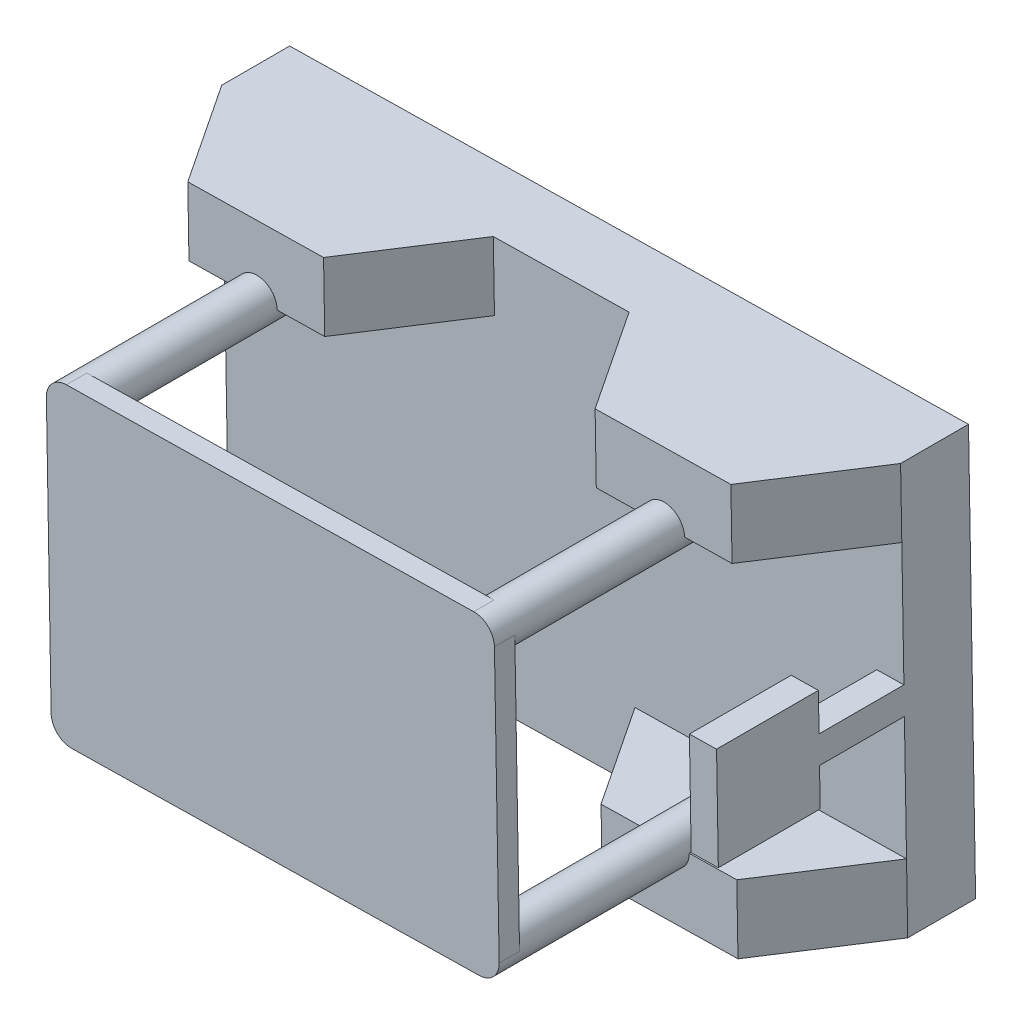
SolidWorks part; units mm, degrees
ref_plane "Front Plane" through (0, 0, 0) normal (0, 0, 1) x (1, 0, 0)
ref_plane "Top Plane" through (0, 0, 0) normal (0, 1, 0) x (1, 0, 0)
ref_plane "Right Plane" through (0, 0, 0) normal (1, 0, 0) x (0, 0, -1)
sketch "Sketch3" plane through (0, 0, 0) normal (0, 0, 1) x (1, 0, 0)
  line L1 (-150, -250) -> (150, -250)
  line L2 (-150, -250) -> (-150, 250)
  line L3 (-150, 250) -> (150, 250)
  line L4 (150, -250) -> (150, 250)
  line L5 (-150, -250) -> (150, 250) construction
  line L6 (-150, 250) -> (150, -250) construction
  point P0 (0, 0)
  dimension "D1" = 300
  dimension "D2" = 500
extrude "Boss-Extrude2" add sketch "Sketch3" along normal blind 50
sketch "Sketch5" plane through (-150, 0, 0) normal (-1, 0, 0) x (0, 0, 1)
  line L0 (0, 0) -> (139.2075, 0) construction
  line L1 (0, 150) -> (139.2075, 150) construction
  line L2 (0, 250) -> (0, -250) construction
  line L3 (0, -150) -> (166.4453, -150) construction
  line L4 (25, 250) -> (25, -250) construction
  line L5 (50, 250) -> (0, 250) construction
  line L6 (50, -250) -> (0, -250) construction
  line L7 (50, 250) -> (125, 200)
  line L8 (125, 200) -> (125, 100)
  line L9 (125, 100) -> (50, 50)
  line L10 (50, 250) -> (50, -250) construction
  line L11 (50, 50) -> (50, 250)
  line L12 (50, -50) -> (50, -250)
  line L13 (125, -100) -> (50, -50)
  line L14 (125, -200) -> (125, -100)
  line L15 (50, -250) -> (125, -200)
  circle A0 centre (25, 150) radius 100 construction
  circle A1 centre (25, -150) radius 100 construction
  dimension "D3" = 200
  dimension "D1" = 150
  dimension "D2" = 150
  dimension "D4" = 200
  dimension "D5" = 100
  dimension "D6" = 100
extrude "Boss-Extrude3" add sketch "Sketch5" against normal blind 50
sketch "Sketch6" plane through (150, 0, 0) normal (1, 0, 0) x (0, 0, -1)
  line L4 (-50, -250) -> (-50, -50)
  line L5 (-125, -200) -> (-50, -250)
  line L6 (-125, -100) -> (-125, -200)
  line L7 (-50, -50) -> (-125, -100)
  line L8 (-50, -250) -> (-50, -50)
  line L9 (-125, -200) -> (-50, -250)
  line L10 (-125, -100) -> (-125, -200)
  line L11 (-50, -50) -> (-125, -100)
  line L12 (-50, 250) -> (-125, 200)
  line L13 (-125, 200) -> (-125, 100)
  line L14 (-125, 100) -> (-50, 50)
  line L15 (-50, 50) -> (-50, 250)
  line L16 (-50, 250) -> (-125, 200)
  line L17 (-125, 200) -> (-125, 100)
  line L18 (-125, 100) -> (-50, 50)
  line L19 (-50, 50) -> (-50, 250)
  dimension "D1" = 0
  dimension "D2" = 0
extrude "Boss-Extrude4" add sketch "Sketch6" against normal blind 50
sketch "Sketch7" plane through (0, 0, 50) normal (0, 0, 1) x (1, 0, 0)
  line L0 (-100, 150) -> (100, 150) construction
  line L1 (-100, 100) -> (-100, 200) construction
  line L2 (100, 200) -> (100, 100) construction
  line L3 (-100, -150) -> (100, -150) construction
  line L4 (-100, -200) -> (-100, -100) construction
  line L5 (100, -250) -> (100, -50) construction
  circle A0 centre (-100, 150) radius 15
  circle A1 centre (100, 150) radius 15
  circle A2 centre (-100, -150) radius 15
  circle A3 centre (100, -150) radius 15
  dimension "D1" = 30
extrude "Boss-Extrude5" add sketch "Sketch7" along normal blind 200
sketch "Sketch8" plane through (0, 0, 250) normal (0, 0, 1) x (1, 0, 0)
  line L1 (-115, -165) -> (115, -165)
  line L2 (-115, -165) -> (-115, 165)
  line L3 (-115, 165) -> (115, 165)
  line L4 (115, -165) -> (115, 165)
  line L5 (-115, -165) -> (115, 165) construction
  line L6 (-115, 165) -> (115, -165) construction
  circle A0 centre (100, -150) radius 15 construction
  circle A1 centre (-100, -150) radius 15 construction
  circle A2 centre (100, 150) radius 15 construction
  circle A3 centre (-100, 150) radius 15 construction
  circle A4 centre (100, -150) radius 15
  circle A5 centre (-100, -150) radius 15
  circle A6 centre (100, 150) radius 15
  circle A7 centre (-100, 150) radius 15
  point P12 (0, 0)
  circle M5 centre (100, -150) radius 15
extrude "Boss-Extrude6" add sketch "Sketch8" along normal blind 15 contours A7 L2 A5 L1 L4 A6 L3 M5 | A7 | A6 | A5 | M5
sketch "Sketch9" plane through (0, 0, 50) normal (0, 0, 1) x (1, 0, 0)
  line L0 (0, 250) -> (0, 165) construction
  line L1 (100, 250) -> (-100, 250) construction
  line L2 (-100, 165) -> (100, 165) construction
  line L4 (-10, 230) -> (10, 230)
  line L5 (-10, 230) -> (-10, 250)
  line L6 (-10, 250) -> (10, 250)
  line L7 (10, 230) -> (10, 250)
  line L8 (-10, 230) -> (10, 250) construction
  line L9 (-10, 250) -> (10, 230) construction
  point P6 (0, 240)
  dimension "D1" = 20
extrude "Boss-Extrude7" add sketch "Sketch9" along normal blind 100
sketch "Sketch10" plane through (0, 250, 0) normal (0, 1, 0) x (1, 0, 0)
  line L0 (10, -150) -> (-10, -150) construction
  line L1 (-37.5, -187.5) -> (37.5, -187.5)
  line L2 (-37.5, -187.5) -> (-37.5, -112.5)
  line L3 (-37.5, -112.5) -> (37.5, -112.5)
  line L4 (37.5, -187.5) -> (37.5, -112.5)
  line L5 (-37.5, -187.5) -> (37.5, -112.5) construction
  line L6 (-37.5, -112.5) -> (37.5, -187.5) construction
  point P0 (0, -150)
  dimension "D1" = 75
extrude "Boss-Extrude8" add sketch "Sketch10" against normal up to surface (20 mm away) up to face at (0, 230, 100)
move or copy body "Body-Move/Copy1" bodies to move or copy 109 copy no rotation origin (0, 0, 0) rotation axis (0, 0, -1) rotation angle 89
